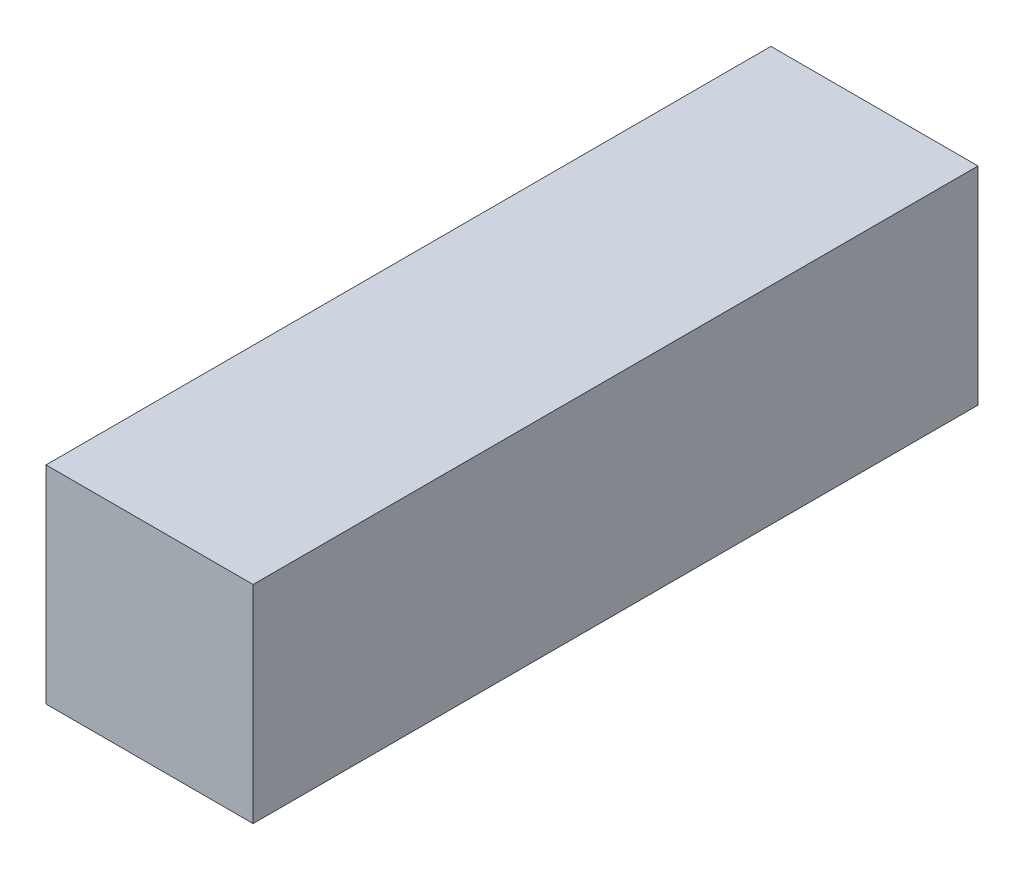
SolidWorks part; units mm, degrees
material "AISI 1020"
ref_plane "Спереди" through (0, 0, 0) normal (0, 0, 1) x (1, 0, 0)
ref_plane "Сверху" through (0, 0, 0) normal (0, 1, 0) x (1, 0, 0)
ref_plane "Справа" through (0, 0, 0) normal (1, 0, 0) x (0, 0, -1)
sketch "Эскиз1" plane through (0, 0, 0) normal (0, 0, 1) x (1, 0, 0)
  line L1 (4, 8.5) -> (-4, 8.5)
  line L2 (4, 8.5) -> (4, 16.5)
  line L3 (4, 16.5) -> (-4, 16.5)
  line L4 (-4, 8.5) -> (-4, 16.5)
  line L5 (4, 8.5) -> (-4, 16.5) construction
  line L6 (4, 16.5) -> (-4, 8.5) construction
  arc A0 (4, 11.8427) -> (-4, 11.8427) centre (0, 0) ccw construction
  point P0 (0, 12.5)
  dimension "D1" = 8
  dimension "D2" = 8
  dimension "D3" = 4
extrude "Бобышка-Вытянуть1" add sketch "Эскиз1" against normal up to vertex (28 mm away) contours L3 L4 L1 L2
